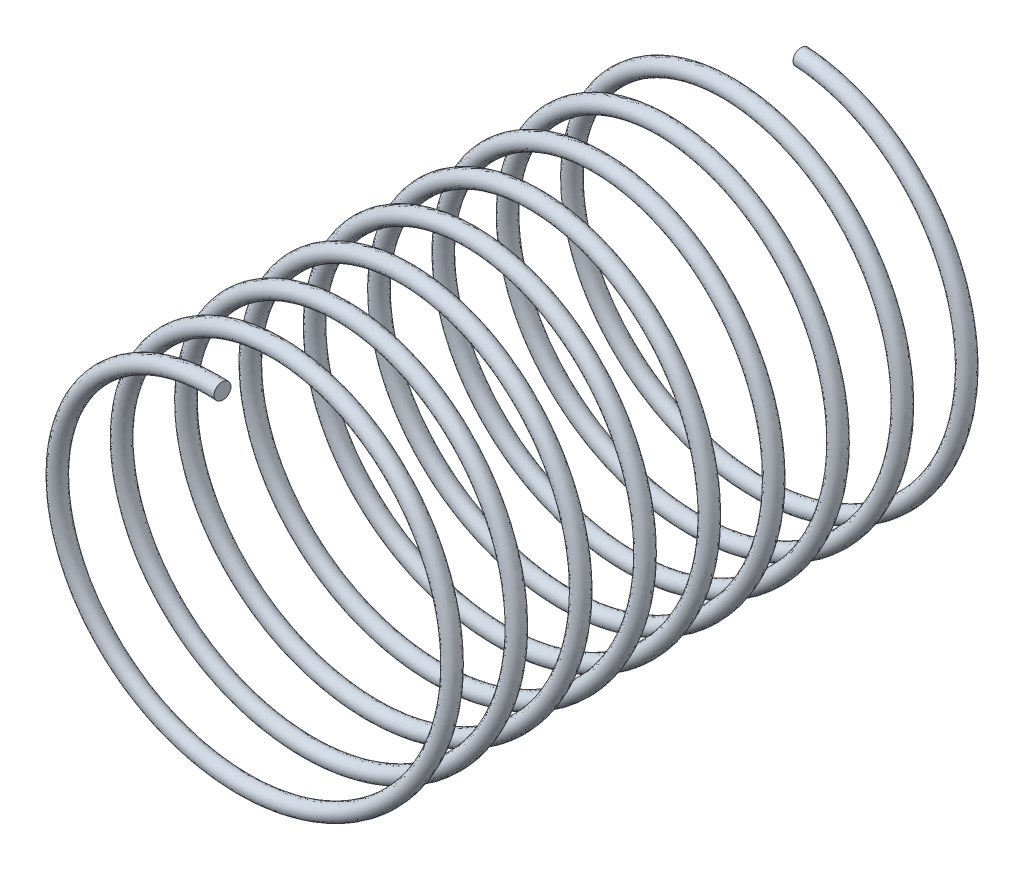
SolidWorks part; units mm, degrees
material "Hexcel AS4C (3000 Filaments)"
ref_plane "Front Plane" through (0, 0, 0) normal (0, 0, 1) x (1, 0, 0)
ref_plane "Top Plane" through (0, 0, 0) normal (0, 1, 0) x (1, 0, 0)
ref_plane "Right Plane" through (0, 0, 0) normal (1, 0, 0) x (0, 0, -1)
sketch "Sketch1" plane through (0, 0, 0) normal (0, 0, 1) x (1, 0, 0)
  circle A0 centre (0, 0) radius 28.575
  dimension "D1" = 57.15
curve "Helix/Spiral1" pitch 10.16 height 91.44 turns 9
sweep "Sweep1" add path "Helix/Spiral1" circular profile diameter 2.54 parameters "D3"=2.54
